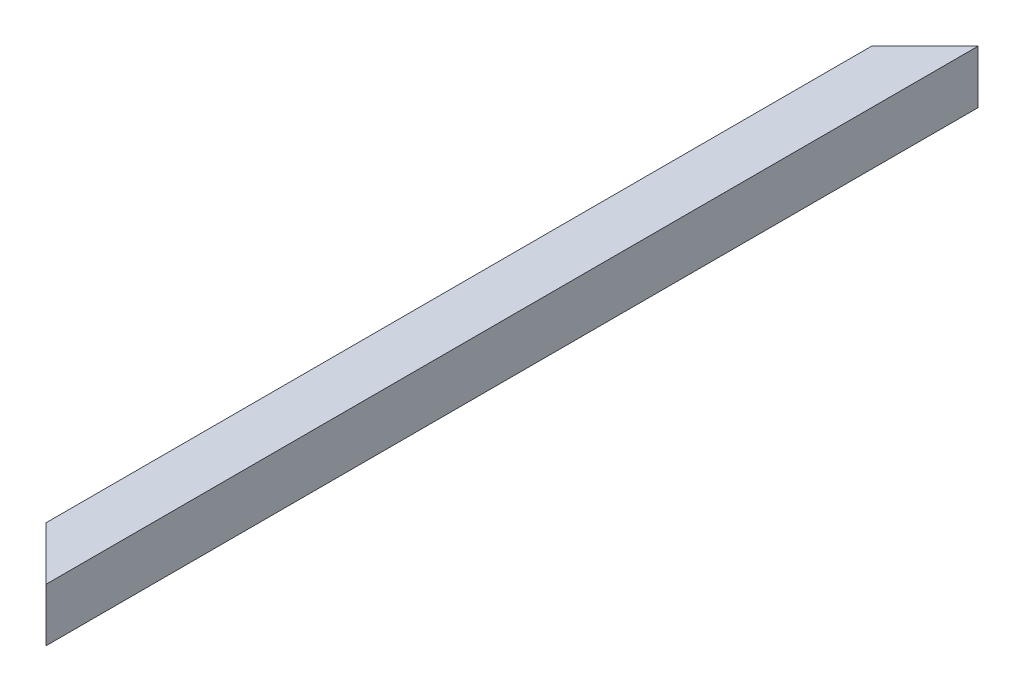
SolidWorks part; units mm, degrees
material "1.0037 (S235JR)"
ref_plane "Front Plane" through (0, 0, 0) normal (0, 0, 1) x (1, 0, 0)
ref_plane "Top Plane" through (0, 0, 0) normal (0, 1, 0) x (1, 0, 0)
ref_plane "Right Plane" through (0, 0, 0) normal (1, 0, 0) x (0, 0, -1)
curve "Curve1"
  spline degree 1 poles (0, 0, 0) (0, 0, 700) knots 0 0 1 1
sketch "Sketch1" plane through (0, 0, 0) normal (0, 0, 1) x (1, 0, 0)
  line L0 (0, 35.3535) -> (0, -33.8384) construction
  line L1 (-20, 20) -> (20, 20)
  line L2 (-20, 20) -> (-20, -20)
  line L3 (-20, -20) -> (20, -20)
  line L4 (20, 20) -> (20, -20)
  line L5 (-16, 16) -> (16, 16)
  line L6 (-16, 16) -> (-16, -16)
  line L7 (-16, -16) -> (16, -16)
  line L8 (16, 16) -> (16, -16)
  line L9 (-39.3939, 0) -> (41.5152, 0) construction
  dimension "40" = 40
  dimension "D2" = 32
sweep "Sweep1" add profiles "Sketch1" path "Curve1"
sketch "Sketch2" plane through (0, 20, 0) normal (0, 1, 0) x (1, 0, 0)
  line L0 (20, 0) -> (-20, -40)
  line L1 (-20, 0) -> (-20, -700) construction
  line L2 (-20, -40) -> (-20, 0)
  line L3 (-20, 0) -> (20, 0)
  line L4 (20, -700) -> (-20, -660)
  line L5 (-20, -660) -> (-20, -700)
  line L6 (-20, -700) -> (20, -700)
  dimension "D1" = 45
  dimension "D2" = 45
extrude "Cut-Extrude1" cut sketch "Sketch2" against normal through all
